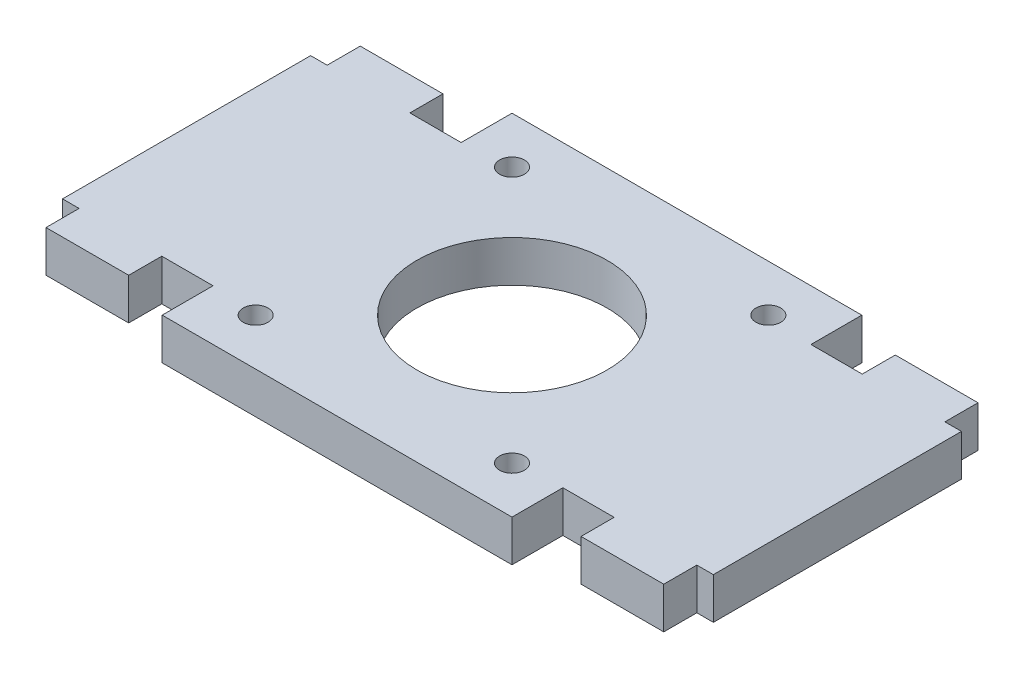
SolidWorks part; units mm, degrees
ref_plane "Front Plane" through (0, 0, 0) normal (0, 0, 1) x (1, 0, 0)
ref_plane "Top Plane" through (0, 0, 0) normal (0, 1, 0) x (1, 0, 0)
ref_plane "Right Plane" through (0, 0, 0) normal (1, 0, 0) x (0, 0, -1)
sketch "Sketch1" plane through (0, 0, 0) normal (0, 1, 0) x (1, 0, 0)
  line L0 (15.5, -15.5) -> (15.5, 15.5) construction
  line L1 (15.5, 15.5) -> (-15.5, 15.5) construction
  line L2 (15.5, 15.5) -> (15.5, -15.5) construction
  line L3 (15.5, -15.5) -> (-15.5, -15.5) construction
  line L4 (-15.5, 15.5) -> (-15.5, -15.5) construction
  line L5 (0, -15.5) -> (0, 15.5)
  line L6 (15.5, 0) -> (-15.5, 0)
  line L7 (15.5, 15.5) -> (-15.5, 15.5) construction
  line L8 (-15.5, -15.5) -> (-15.5, 15.5) construction
  line L9 (15.5, -15.5) -> (-15.5, -15.5) construction
  line L10 (-15.5, -15.5) -> (15.5, -15.5) construction
  line L11 (15.5, -15.5) -> (15.5, 15.5) construction
  line L12 (-15.5, 15.5) -> (15.5, 15.5) construction
  line L13 (-15.5, -15.5) -> (-15.5, 15.5) construction
  line L14 (-15.5, 15.5) -> (-15.5, -15.5) construction
  line L15 (-15.5, -15.5) -> (15.5, -15.5) construction
  line L16 (15.5, 15.5) -> (15.5, -15.5) construction
  line L17 (-15.5, 15.5) -> (15.5, 15.5) construction
  line L18 (-39.35, -15) -> (-37.35, -15)
  line L19 (-21.15, 21.15) -> (21.15, 21.15)
  line L20 (-39.35, 15) -> (-39.35, -15)
  line L21 (-21.15, -21.15) -> (21.15, -21.15)
  line L22 (39.35, 15) -> (39.35, -15)
  line L23 (0, -21.15) -> (0, 21.15) construction
  line L24 (-39.35, 0) -> (39.35, 0) construction
  line L25 (-37.35, -15) -> (-37.35, -19)
  line L26 (-39.35, 15) -> (-37.35, 15)
  line L27 (-37.35, 15) -> (-37.35, 19)
  line L28 (39.35, 15) -> (37.35, 15)
  line L29 (37.35, 15) -> (37.35, 19)
  line L30 (39.35, -15) -> (37.35, -15)
  line L31 (37.35, -15) -> (37.35, -19)
  line L32 (37.35, -19) -> (27.35, -19)
  line L33 (27.35, -19) -> (27.35, -15)
  line L34 (27.35, -15) -> (21.15, -15)
  line L35 (21.15, -15) -> (21.15, -21.15)
  line L36 (37.35, 19) -> (27.35, 19)
  line L37 (27.35, 19) -> (27.35, 15)
  line L38 (27.35, 15) -> (21.15, 15)
  line L39 (-37.35, 19) -> (-27.35, 19)
  line L40 (-27.35, 19) -> (-27.35, 15)
  line L41 (-27.35, 15) -> (-21.15, 15)
  line L42 (-37.35, -19) -> (-27.35, -19)
  line L43 (-27.35, -19) -> (-27.35, -15)
  line L44 (-27.35, -15) -> (-21.15, -15)
  line L45 (-21.15, 15) -> (-21.15, 21.15)
  line L46 (21.15, 15) -> (21.15, 21.15)
  line L47 (-21.15, -15) -> (-21.15, -21.15)
  circle A0 centre (0, 0) radius 11.5
  circle A1 centre (15.5, 15.5) radius 1.5
  circle A2 centre (15.5, -15.5) radius 1.5
  circle A3 centre (-15.5, -15.5) radius 1.5
  circle A4 centre (-15.5, 15.5) radius 1.5
  point P32 (0, 0)
  point P99 (0, 0)
  point P235 (0, 0)
  dimension "D1" = 23
  dimension "D3" = 3
  dimension "D2" = 31
  dimension "D4" = 4
  dimension "D5" = 10
  dimension "D6" = 4
  dimension "D7" = 2
  dimension "D8" = 42.3
  dimension "D9" = 2
  dimension "D10" = 78.7
  dimension "D11" = 2
  dimension "D12" = 42.3
  dimension "D13" = 2
  dimension "D14" = 10
  dimension "D15" = 6.2
  dimension "D16" = 4
  dimension "D17" = 30
  dimension "D18" = 4
  dimension "D19" = 6.2
  dimension "D20" = 10
  dimension "D21" = 4
  dimension "D22" = 6.2
  dimension "D23" = 10
  dimension "D24" = 4
  dimension "D25" = 6.2
  dimension "D26" = 4
  dimension "D27" = 4
  dimension "D28" = 4
  dimension "D29" = 6.15
extrude "Boss-Extrude1" add sketch "Sketch1" along normal blind 5
